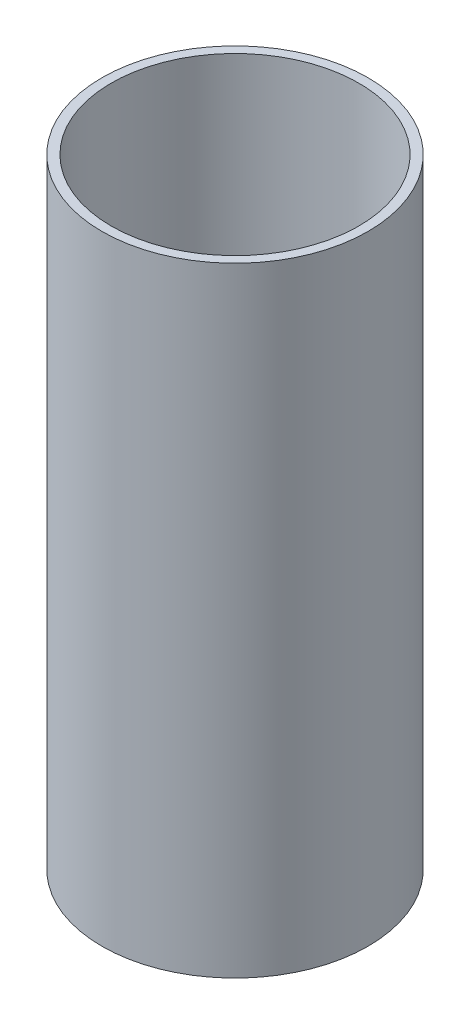
SolidWorks part; units mm, degrees
ref_plane "Front Plane" through (0, 0, 0) normal (0, 0, 1) x (1, 0, 0)
ref_plane "Top Plane" through (0, 0, 0) normal (0, 1, 0) x (1, 0, 0)
ref_plane "Right Plane" through (0, 0, 0) normal (1, 0, 0) x (0, 0, -1)
sketch "Sketch1" plane through (0, 0, 0) normal (0, 1, 0) x (1, 0, 0)
  circle A0 centre (0, 0) radius 25.4
  circle A1 centre (0, 0) radius 27.305
  dimension "D1" = 54.61
  dimension "D2" = 50.8
extrude "Boss-Extrude1" add sketch "Sketch1" along normal blind 127
